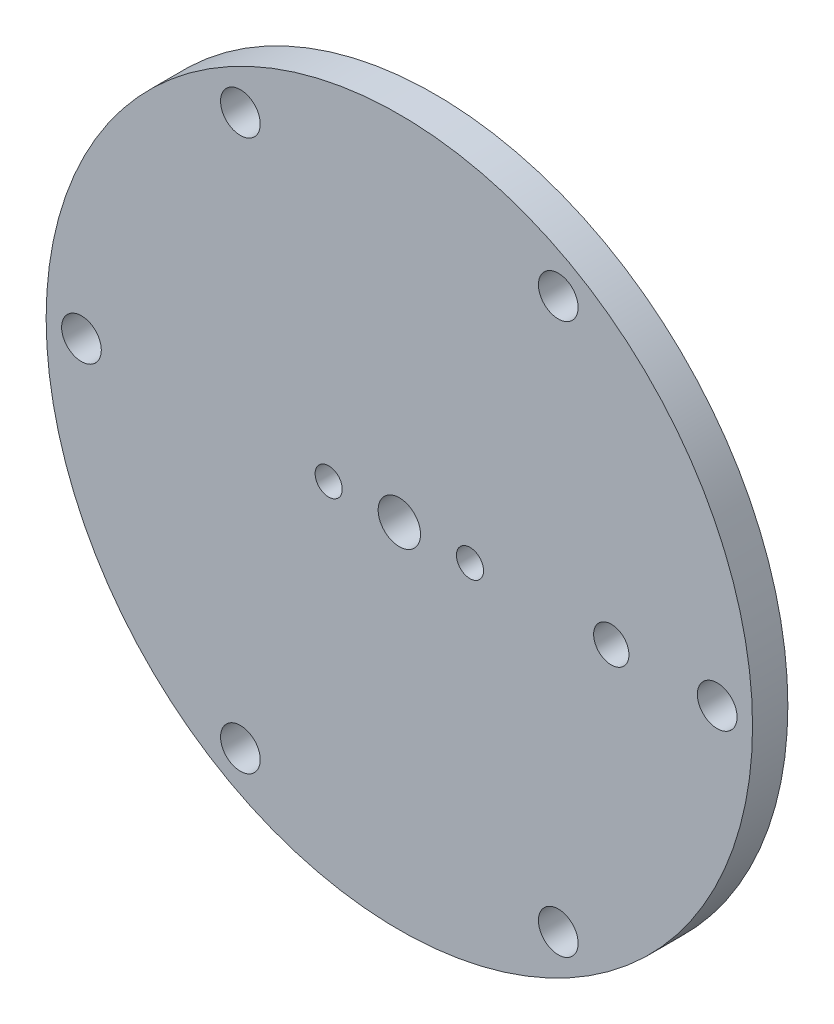
SolidWorks part; units mm, degrees
ref_plane "Front Plane" through (0, 0, 0) normal (0, 0, 1) x (1, 0, 0)
ref_plane "Top Plane" through (0, 0, 0) normal (0, 1, 0) x (1, 0, 0)
ref_plane "Right Plane" through (0, 0, 0) normal (1, 0, 0) x (0, 0, -1)
sketch "Sketch1" plane through (0, 0, 0) normal (0, 0, 1) x (1, 0, 0)
  circle A0 centre (0, 0) radius 31.75
  dimension "D1" = 63.5
extrude "Boss-Extrude1" add sketch "Sketch1" along normal blind 3.175
hole_wizard "#28 (0.1405) Diameter Hole1" positions "Sketch3" profile "Sketch4" hole size "#28" standard "ANSI Inch"
sketch "Sketch3" plane through (0, 0, 3.175) normal (0, 0, 1) x (1, 0, 0)
  line L0 (0, 0) -> (19.7944, 34.2849) construction
  line L3 (0, 0) -> (45.5277, 0) construction
  point P0 (14.2875, 24.7467)
  dimension "D1" = 28.575
  dimension "D2" = 60
sketch "Sketch4" plane through (14.2875, 24.7467, 3.175) normal (1, 0, 0) x (0, -1, 0)
  line L0 (0, 0) -> (0, 26.4721)
  line L1 (0, 26.4721) -> (1.7843, 25.4)
  line L2 (1.7843, 25.4) -> (1.7843, 0)
  line L5 (1.7843, 0) -> (0, 0)
  line L10 (0, 26.4721) -> (-1.7844, 25.4) construction
  line L11 (0, -6.35) -> (0, 107.95) construction
  dimension "Hole Dia." = 3.5687
  dimension "Hole Depth" = 25.4
  dimension "Drill Angle" = 118
pattern_circular "CirPattern1" count 6 over 360 about axis through (0, 0, 0) along (0, 0, 1) of "#28 (0.1405) Diameter Hole1"
sketch "Sketch5" plane through (0, 0, 3.175) normal (0, 0, 1) x (1, 0, 0)
  circle A0 centre (0, 0) radius 1.905
  dimension "D1" = 3.81
extrude "Cut-Extrude1" cut sketch "Sketch5" against normal through all
hole_wizard "CSK for #2 Flat Head Machine Screw (100)1" positions "Sketch7" profile "Sketch6" countersink size "#2" standard "ANSI Inch" end condition through all
sketch "Sketch7" plane through (0, 0, 0) normal (0, 0, -1) x (-1, 0, 0)
  point P0 (6.35, 0)
  point P2 (-6.35, 0)
  dimension "D1" = 6.35
  dimension "D2" = 6.35
sketch "Sketch6" plane through (-6.35, 0, 0) normal (1, 0, 0) x (0, 1, 0)
  line L0 (0, 0) -> (0, 3.175)
  line L1 (0, 3.175) -> (1.2192, 3.175)
  line L2 (1.2192, 3.175) -> (1.2192, 0.8099)
  line L3 (1.2192, 0.8099) -> (2.1844, 0)
  line L5 (2.1844, 0) -> (0, 0)
  line L6 (-1.2192, 0.8099) -> (-2.1844, 0) construction
  line L11 (0, -6.35) -> (0, 107.95) construction
  dimension "Thru Hole Dia." = 2.4384
  dimension "Thru Hole Depth" = 3.175
  dimension "Near C'Sink Dia." = 4.3688
  dimension "Near C'Sink Angle" = 100
sketch "Sketch8" plane through (0, 0, 3.175) normal (0, 0, 1) x (1, 0, 0)
  line L0 (0, 0) -> (28.575, 0) construction
  circle A0 centre (19.05, 0) radius 1.5875
  dimension "D2" = 3.175
  dimension "D1" = 19.05
extrude "Cut-Extrude2" cut sketch "Sketch8" against normal through all
equation "\"D2@Sketch7\"=\"D1@Sketch7\""
